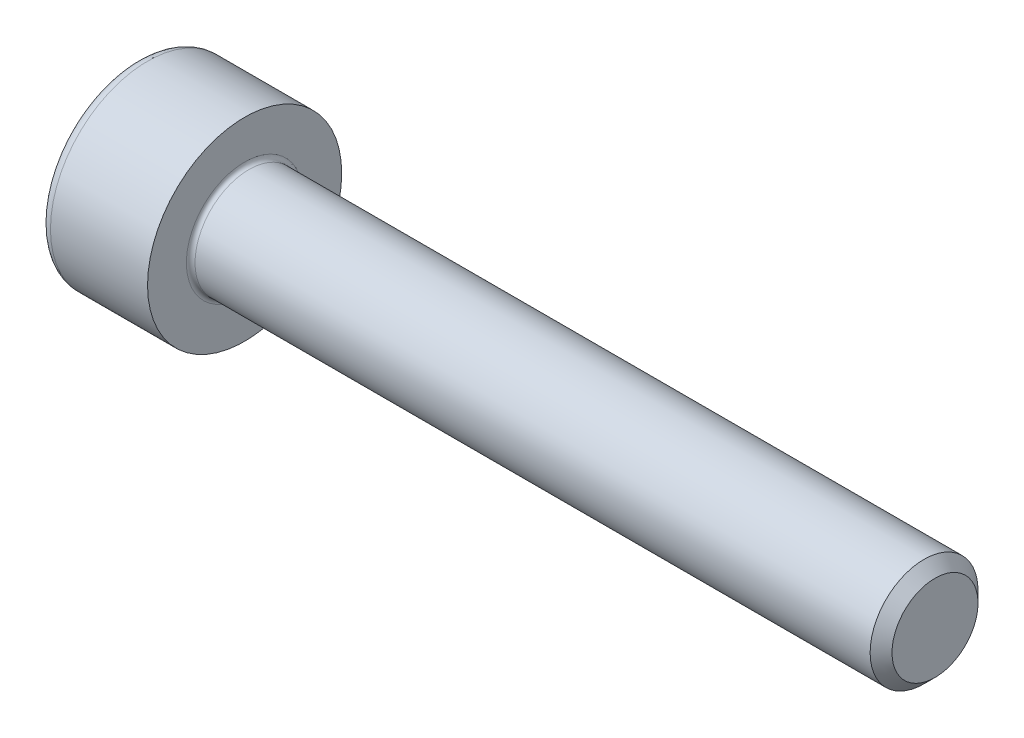
SolidWorks part; units mm, degrees
revolve "Base-Revolve" add sketch "BodySke"
sketch "BodySke" plane through (0, 0, 0) normal (0, 0, 1) x (1, 0, 0)
  line L0 (0, 0) -> (0, 2.25)
  line L1 (0, 2.25) -> (2.5, 2.25)
  line L2 (2.5, 2.25) -> (2.5, 1.25)
  line L3 (2.5, 1.25) -> (18.2465, 1.25)
  line L4 (18.5, 0.9965) -> (18.5, 0)
  line L5 (18.5, 0) -> (0, 0)
  line L6 (-31.75, 0) -> (127, 0) construction
  line L8 (18.5, 0.9965) -> (18.2465, 1.25)
  line L10 (18.5, -0.9965) -> (18.2465, -1.25) construction
  line L11 (2.95, 9.525) -> (2.95, 3.175) construction
  line L12 (2.5, 9.525) -> (2.5, 3.175) construction
  line L13 (-41.5, 9.525) -> (-41.5, 3.175) construction
  dimension "Head_ht" = 2.5
  dimension "Length" = 16
  dimension "Body_ch_ang" = 45
  dimension "Diameter" = 2.5
  dimension "Minor_dia" = 1.993
  dimension "Advance" = 0.45
  dimension "Thread_nom" = 16
  dimension "Thread_length" = 60
  dimension "Head_dia" = 4.5
cosmetic thread "ThreadCosmetic"
fillet "Fillet1" radius 0.1 1 edges at (2.5, 0, 1.25)
fillet "Fillet2" radius 0.25 1 edges at (0, 0, 2.25)
ref_plane "Plane1" through (0, 0, 0) normal (0, 0, 1) x (1, 0, 0)
ref_plane "Plane2" through (0, 0, 0) normal (0, 1, 0) x (1, 0, 0)
ref_plane "Plane3" through (0, 0, 0) normal (1, 0, 0) x (0, 0, -1)
sketch "Sketch2" plane through (0, 0, 0) normal (0, 0, 1) x (1, 0, 0)
  line L0 (0, 1.01) -> (1.1, 1.01)
  line L1 (1.1, 1.01) -> (1.6831, 0)
  line L2 (-31.75, 0) -> (127, 0) construction
  line L3 (1.6831, 0) -> (0, 0)
  line L4 (0, 0) -> (0, 1.01)
  line L6 (0, 0) -> (47.625, 0) construction
  dimension "D1" = 1.01
  dimension "D2" = 60
  dimension "Depth" = 1.1
revolve "Hex-PreBroach" cut sketch "Sketch2" angle 360 about L6
sketch "Sketch3" plane through (0, 0, 0) normal (-1, 0, 0) x (0, 0.5, 0.866)
  line L0 (0.5831, 1.01) -> (-0.5831, 1.01)
  line L1 (-0.5831, 1.01) -> (-1.1662, 0)
  line L2 (0.5831, 1.01) -> (1.1662, 0)
  line L3 (0.5831, -1.01) -> (1.1662, 0)
  line L4 (0.5831, -1.01) -> (-0.5831, -1.01)
  line L5 (-0.5831, -1.01) -> (-1.1662, 0)
  dimension "D1" = 1.01
  dimension "D2" = 1.01
  dimension "Hex_size" = 2.02
extrude "Hex" cut sketch "Sketch3" against normal blind 1.1
sketch "ThdSchSke" plane through (0, 0, 0) normal (0, 0, 1) x (1, 0, 0)
  line L0 (3.85, -0.9965) -> (3.6725, -1.25)
  line L1 (3.85, -0.9965) -> (4.0275, -1.25)
  line L2 (4.0275, -1.25) -> (4.0275, -1.5625)
  line L3 (-3.175, 0) -> (5.1513, 0) construction
  line L4 (0, 2) -> (0, -2) construction
  line L5 (4.0275, -1.5625) -> (3.6725, -1.5625)
  line L6 (3.6725, -1.5625) -> (3.6725, -1.25)
  dimension "Thread_minor" = 1.993
  dimension "Diameter" = 2.5
  dimension "Start" = 3.85
revolve "ThreadSchematic" [suppressed] cut sketch "ThdSchSke" angle 360 about L3
pattern_linear "ThdSchPat" [suppressed]
equation "\"D2@Sketch3\" = \"Hex_size@Sketch3\" / 2"
equation "\"D1@Sketch3\" = \"Hex_size@Sketch3\" / 2"
equation "\"D1@Sketch2\" = \"Hex_size@Sketch3\" / 2"
equation "\"Thread_minor@ThreadCosmetic\"  =  \"Minor_dia@BodySke\""
equation "\"Depth@Sketch2\" =  \"Key_eng@Hex\""
equation "\"Thread_length@ThreadCosmetic\" = ((sgn( (\"Length@BodySke\" - \"Advance@BodySke\" * 3.0) - \"Thread_nom@BodySke\" )-1)*( (\"Length@BodySke\" - \"Advance@BodySke\" * 3.0) - \"Thread_nom@BodySke\" ))/-2+ \"Thread_nom@BodySke\""
equation "\"Thread_minor@ThdSchSke\" = \"Minor_dia@BodySke\""
equation "\"Diameter@ThdSchSke\" = \"Diameter@BodySke\""
equation "\"Overcut@ThdSchSke\" = \"Diameter@BodySke\" * 1.25"
equation "\"Start@ThdSchSke\" = \"Head_ht@BodySke\" + \"Length@BodySke\" - \"Thread_length@ThreadCosmetic\"  '---Non-countersunk---"
equation "\"Num_threads@ThdSchPat\" = int( \"Thread_length@ThreadCosmetic\" / \"Advance@BodySke\" + 0.999 )  + 1"
equation "\"Advance@ThdSchPat\" = \"Thread_length@ThreadCosmetic\" /  (\"Num_threads@ThdSchPat\" - 1) 'relax it"
equation "\"Num_threads@ThdSchPat\" = \"Num_threads@ThdSchPat\" - sgn( \"Num_threads@ThdSchPat\" - 1) '---chamfered tips only---"
